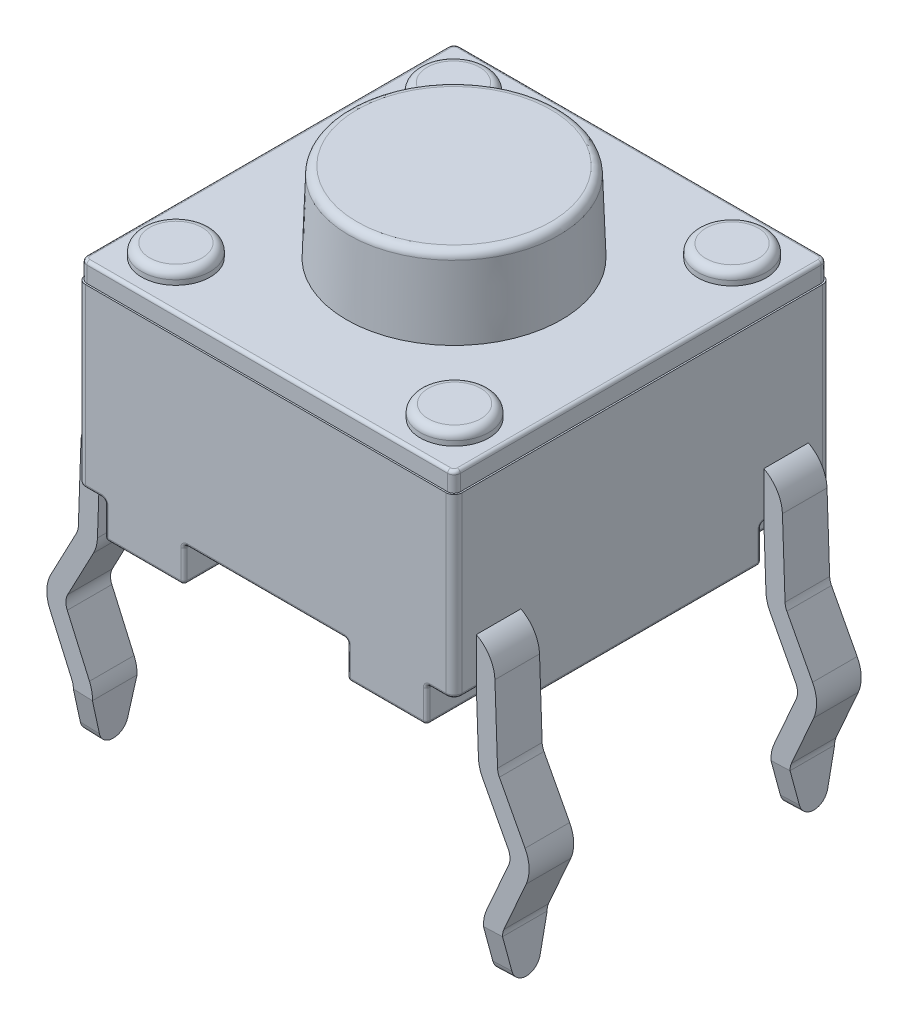
SolidWorks part; units mm, degrees
ref_plane "Front Plane" through (0, 0, 0) normal (0, 0, 1) x (1, 0, 0)
ref_plane "Top Plane" through (0, 0, 0) normal (0, 1, 0) x (1, 0, 0)
ref_plane "Right Plane" through (0, 0, 0) normal (1, 0, 0) x (0, 0, -1)
sketch "Sketch1" plane through (0, 0, 0) normal (0, 1, 0) x (1, 0, 0)
  line L1 (-3.0035, -3.0035) -> (3.0035, -3.0035)
  line L2 (-3.0035, -3.0035) -> (-3.0035, 3.0036)
  line L3 (-3.0035, 3.0036) -> (3.0035, 3.0036)
  line L4 (3.0035, -3.0035) -> (3.0035, 3.0036)
  line L5 (-3.0035, -3.0035) -> (3.0035, 3.0036) construction
  line L6 (-3.0035, 3.0036) -> (3.0035, -3.0035) construction
  point P0 (0, 0)
  dimension "D1" = 6.0071
  dimension "D2" = 6.0071
extrude "Boss-Extrude1" add sketch "Sketch1" along normal blind 2.8194 from offset 0.5588
fillet "Fillet1" radius 0.127 4 edges at (-3.0035, 1.9685, 3.0035) (-3.0035, 1.9685, -3.0036) (3.0035, 1.9685, -3.0036) (3.0035, 1.9685, 3.0035)
sketch "Sketch2" plane through (0, 3.3782, 0) normal (0, -1, 0) x (-1, 0, 0)
  line L8 (2.9781, -2.8765) -> (2.9781, 2.8765)
  line L9 (-2.8765, -2.9781) -> (2.8765, -2.9781)
  line L10 (-2.9781, 2.8765) -> (-2.9781, -2.8765)
  line L11 (2.8765, 2.9782) -> (-2.8765, 2.9782)
  line L12 (2.9781, -2.8765) -> (2.9781, 2.8765)
  line L13 (-2.8765, -2.9781) -> (2.8765, -2.9781)
  line L14 (-2.9781, 2.8765) -> (-2.9781, -2.8765)
  line L15 (2.8765, 2.9782) -> (-2.8765, 2.9782)
  arc A8 (2.8765, -2.9781) -> (2.9781, -2.8765) centre (2.8765, -2.8765) ccw
  arc A9 (-2.9781, -2.8765) -> (-2.8765, -2.9781) centre (-2.8765, -2.8765) ccw
  arc A10 (-2.8765, 2.9782) -> (-2.9781, 2.8765) centre (-2.8765, 2.8766) ccw
  arc A11 (2.9781, 2.8765) -> (2.8765, 2.9782) centre (2.8765, 2.8765) ccw
  arc A12 (2.8765, -2.9781) -> (2.9781, -2.8765) centre (2.8765, -2.8765) ccw
  arc A13 (-2.9781, -2.8765) -> (-2.8765, -2.9781) centre (-2.8765, -2.8765) ccw
  arc A14 (-2.8765, 2.9782) -> (-2.9781, 2.8765) centre (-2.8765, 2.8766) ccw
  arc A15 (2.9781, 2.8765) -> (2.8765, 2.9782) centre (2.8765, 2.8765) ccw
  dimension "D1" = 0.0254
extrude "Boss-Extrude2" add sketch "Sketch2" against normal blind 0.3048
sketch "Sketch3" plane through (0, 0, 0) normal (0, 1, 0) x (1, 0, 0)
  line L0 (-2.5662, -3.0035) -> (-2.5662, -1.8948)
  line L1 (-2.8765, -3.0035) -> (2.8765, -3.0035) construction
  line L2 (-2.5662, -1.8948) -> (-3.0035, -1.8948)
  line L3 (-3.0035, 2.8765) -> (-3.0035, -2.8765) construction
  line L4 (-2.4413, -0.5609) -> (-1.3018, -0.5609)
  line L5 (-1.3018, -0.5609) -> (-1.3017, -3.0035)
  line L6 (-2.4413, -0.5609) -> (-2.4413, 0.5609)
  line L7 (-2.5662, -3.0035) -> (-1.3017, -3.0035)
  line L8 (-3.0035, -1.8948) -> (-3.0035, 1.8948)
  line L9 (-2.4413, 0) -> (-3.0035, 0) construction
  line L10 (-2.5662, 3.0036) -> (-1.3017, 3.0035)
  line L11 (-1.3017, 0.5609) -> (-1.3017, 3.0035)
  line L12 (-2.4413, 0.5609) -> (-1.3017, 0.5609)
  line L13 (-2.5662, 1.8948) -> (-3.0035, 1.8948)
  line L14 (-2.5662, 3.0036) -> (-2.5662, 1.8948)
  line L15 (0, -3.0035) -> (0, 3.0036) construction
  line L16 (2.8765, 3.0036) -> (-2.8765, 3.0036) construction
  line L17 (2.4413, 0) -> (3.0035, 0) construction
  line L18 (2.5662, 3.0035) -> (2.5662, 1.8948)
  line L19 (2.5662, 1.8948) -> (3.0035, 1.8948)
  line L20 (2.4413, 0.5609) -> (1.3017, 0.5609)
  line L21 (1.3017, 0.5609) -> (1.3017, 3.0035)
  line L22 (2.5662, 3.0035) -> (1.3017, 3.0035)
  line L23 (3.0035, -1.8948) -> (3.0035, 1.8948)
  line L24 (2.5662, -3.0036) -> (1.3017, -3.0036)
  line L25 (2.4413, -0.5609) -> (2.4413, 0.5609)
  line L26 (1.3017, -0.5609) -> (1.3017, -3.0036)
  line L27 (2.4413, -0.5609) -> (1.3017, -0.5609)
  line L28 (2.5662, -1.8948) -> (3.0035, -1.8948)
  line L29 (2.5662, -3.0036) -> (2.5662, -1.8948)
  dimension "D1" = 1.7018
extrude "Boss-Extrude3" add sketch "Sketch3" along normal up to next
sketch "Sketch4" plane through (0, 3.683, 0) normal (0, 1, 0) x (1, 0, 0)
  line L1 (-2.2217, -2.2129) -> (2.2217, -2.2129) construction
  line L2 (-2.2217, -2.2129) -> (-2.2217, 2.2129) construction
  line L3 (-2.2217, 2.2129) -> (2.2217, 2.2129) construction
  line L4 (2.2217, -2.2129) -> (2.2217, 2.2129) construction
  line L5 (-2.2217, -2.2129) -> (2.2217, 2.2129) construction
  line L6 (-2.2217, 2.2129) -> (2.2217, -2.2129) construction
  circle A0 centre (2.2217, 2.2129) radius 0.5461
  circle A1 centre (-2.2217, 2.2129) radius 0.5461
  circle A2 centre (-2.2217, -2.2129) radius 0.5461
  circle A3 centre (2.2217, -2.2129) radius 0.5461
  point P0 (0, 0)
  dimension "D1" = 1.0922
extrude "Boss-Extrude4" add sketch "Sketch4" along normal blind 0.2032
sketch "Sketch5" plane through (0, 3.683, 0) normal (0, 1, 0) x (1, 0, 0)
  circle A0 centre (0, 0) radius 1.7145
  dimension "D1" = 3.429
extrude "Boss-Extrude5" add sketch "Sketch5" along normal blind 1.27 draft 2
fillet "Fillet2" radius 0.127 5 edges at (-2.2217, 3.8862, -1.6668) (-2.2217, 3.8862, 2.759) (2.2217, 3.8862, -1.6668) (2.2217, 3.8862, 2.759) (0, 4.953, 1.6702)
fillet "Fillet3" radius 0.0508 88 edges at (2.9664, 0.5588, 2.9664) (2.9664, 0.5588, -2.9664) (-2.9664, 0.5588, -2.9664) (-2.9664, 0.5588, 2.9664) (3.0035, 0.5588, 2.3857) (3.0035, 0.5588, -2.3857) (1.3017, 0.2794, 3.0036) (1.3017, 0.2794, -3.0035) (2.9484, 3.683, -2.9484) (0, 3.683, -2.9782) (-2.9484, 3.683, -2.9484) (-2.9781, 3.683, 0) (-2.9484, 3.683, 2.9484) (0, 3.683, 2.9781) (2.9484, 3.683, 2.9484) (2.4413, 0.2794, 0.5609) (1.3017, 0.2794, 0.5609) (1.3017, 0.2794, -0.5609) (2.4413, 0.2794, -0.5609) (-1.3018, 0.2794, 0.5609) (-2.4413, 0.2794, 0.5609) (-2.4413, 0.2794, -0.5609) (-1.3017, 0.2794, -0.5609) (2.7849, 0.5588, 1.8948) (3.0035, 0.2794, 1.8948) (2.5662, 0.2794, 3.0036) (2.5662, 0.5588, 2.4492) (2.5662, 0.2794, 1.8948) (3.0035, 0.2794, -1.8948) (2.7849, 0.5588, -1.8948) (2.5662, 0.2794, -1.8948) (2.5662, 0.5588, -2.4492) (2.5662, 0.2794, -3.0035) (-2.5662, 0.2794, -1.8948) (-2.5662, 0.2794, 1.8948) (-1.8715, 0.5588, -0.5609) (-2.4413, 0.5588, 0) (-1.8715, 0.5588, 0.5609) (1.3017, 0.5588, 1.7822) (1.8715, 0.5588, 0.5609) (2.4413, 0.5588, 0) (1.8715, 0.5588, -0.5609) (1.3017, 0.5588, -1.7822) (-1.3017, 0, 1.7822) (-1.8715, 0, 0.5609) (-2.4413, 0, 0) (-1.8715, 0, -0.5609) (-1.3017, 0, -1.7822) (-1.934, 0, -3.0035) (-2.5662, 0, -2.4492) (-2.7849, 0, -1.8948) (-3.0035, 0, 0) (-2.7849, 0, 1.8948) (-2.5662, 0, 2.4492) (-1.934, 0, 3.0035) (1.3017, 0, -1.7822) (1.8715, 0, -0.5609) (2.4413, 0, 0) (1.8715, 0, 0.5609) (1.3017, 0, 1.7822) (1.934, 0, 3.0036) (2.5662, 0, 2.4492) (2.7849, 0, 1.8948) (3.0035, 0, 0) (2.7849, 0, -1.8948) (2.5662, 0, -2.4492) (1.934, 0, -3.0035) (2.9781, 3.683, 0)
sketch "Sketch6" plane through (0, 0, 3.0035) normal (0, 0, 1) x (1, 0, 0)
  line L0 (-2.9873, 1.0641) -> (-3.0423, -0.5107)
  line L1 (-3.0423, -0.5107) -> (-3.5687, -1.5089)
  line L2 (-3.5687, -1.5089) -> (-3.1132, -2.5415)
  line L3 (-3.1132, -2.5415) -> (-3.1424, -3.3782)
  line L4 (-2.9873, 1.0641) -> (-2.5265, 1.0641)
  line L5 (-1.3525, 0) -> (-2.5154, 0) construction
  dimension "D1" = 4.445
  dimension "D2" = 3.3782
  dimension "D3" = 3.0226
  dimension "D4" = 3.5687
  dimension "D5" = 2.032
  dimension "D6" = 1.5748
  dimension "D7" = 92
extrude "Extrude-Thin1" add sketch "Sketch6" against normal blind 0.7112 from offset 0.3556 thin offset against normal yes
sketch "Sketch9" plane through (-3.3254, 0.1161, 0) normal (-0.9994, 0.0349, 0) x (0, 0, 1)
  line L0 (2.6479, -2.7766) -> (2.5175, -3.3091)
  line L1 (2.0672, -3.3091) -> (1.9367, -2.7766)
  line L2 (1.9367, -3.4858) -> (2.6479, -3.4858) construction
  line L3 (2.6479, -2.7766) -> (2.6479, -3.4858)
  line L4 (2.6479, -3.4858) -> (1.9367, -3.4858)
  line L5 (1.9367, -3.4858) -> (1.9367, -2.7766)
  arc A0 (2.5175, -3.3091) -> (2.0672, -3.3091) centre (2.2923, -3.254) cw
  line M1 (2.6479, -3.4858) -> (2.6479, -2.7766)
  line M3 (1.9367, -2.7766) -> (1.9367, -3.4858)
  line M4 (1.9367, -3.4858) -> (2.6479, -3.4858)
extrude "Cut-Extrude1" cut sketch "Sketch9" against normal blind 0.7112 contours L0 A0 L4 M1 | A0 L1 M4 M3
mirror "Mirror1" about plane through (0, 0, 0) normal (0, 0, 1) of "Cut-Extrude1", "Extrude-Thin1"
mirror "Mirror3" about plane through (0, 0, 0) normal (1, 0, 0) of "Mirror1", "Cut-Extrude1", "Extrude-Thin1"
